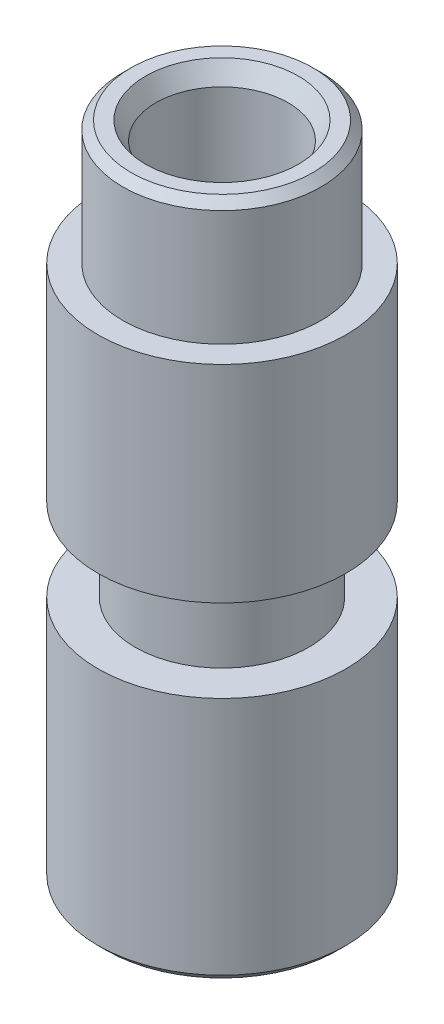
SolidWorks part; units mm, degrees
ref_plane "Front Plane" through (0, 0, 0) normal (0, 0, 1) x (1, 0, 0)
ref_plane "Top Plane" through (0, 0, 0) normal (0, 1, 0) x (1, 0, 0)
ref_plane "Right Plane" through (0, 0, 0) normal (1, 0, 0) x (0, 0, -1)
sketch "Sketch1" plane through (0, 0, 0) normal (0, 1, 0) x (1, 0, 0)
  circle A0 centre (0, 0) radius 3
  dimension "D1" = 6
extrude "Boss-Extrude1" add sketch "Sketch1" along normal blind 6
cosmetic thread "Rosca cosmética1" parameters "D2"=5
sketch "Sketch2" plane through (0, 6, 0) normal (0, 1, 0) x (1, 0, 0)
  circle A0 centre (0, 0) radius 2.1
  dimension "D1" = 4.2
extrude "Boss-Extrude2" add sketch "Sketch2" along normal blind 2
sketch "Sketch3" plane through (0, 8, 0) normal (0, 1, 0) x (1, 0, 0)
  circle A0 centre (0, 0) radius 3
  dimension "D1" = 6
extrude "Boss-Extrude3" add sketch "Sketch3" along normal blind 5
cosmetic thread "Rosca cosmética2" parameters "D2"=5
sketch "Sketch4" plane through (0, 13, 0) normal (0, 1, 0) x (1, 0, 0)
  circle A0 centre (0, 0) radius 1.6
  dimension "D1" = 3.2
extrude "Cut-Extrude1" cut sketch "Sketch4" against normal through all
sketch "Croquis1" plane through (0, 13, 0) normal (0, 1, 0) x (1, 0, 0)
  circle A0 centre (0, 0) radius 2.4
  circle A1 centre (0, 0) radius 1.6
  circle A2 centre (0, 0) radius 1.6 construction
  dimension "D1" = 4.8
extrude "Saliente-Extruir1" add sketch "Croquis1" along normal blind 3
chamfer "Chaflán1" distance 0.2 angle 45 1 edges at (0, 16, 2.4)
chamfer "Chaflán2" distance 0.2 angle 45 1 edges at (0, 0, 3)
chamfer "Chaflán3" distance 0.25 angle 60 1 edges at (0, 16, 1.6)
